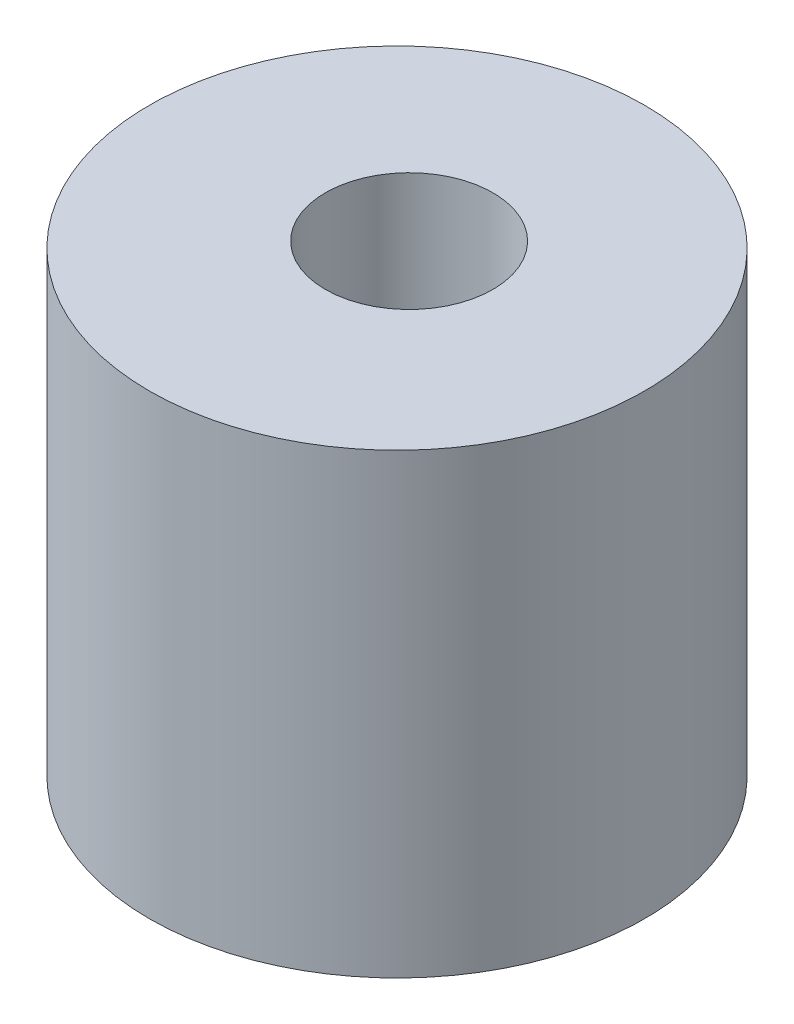
SolidWorks part; units mm, degrees
ref_plane "Plan de face" through (0, 0, 0) normal (0, 0, 1) x (1, 0, 0)
ref_plane "Plan de dessus" through (0, 0, 0) normal (0, 1, 0) x (1, 0, 0)
ref_plane "Plan de droite" through (0, 0, 0) normal (1, 0, 0) x (0, 0, -1)
sketch "Esquisse1" plane through (0, 0, 0) normal (0, 1, 0) x (1, 0, 0)
  circle A0 centre (0, 0) radius 3.25
  circle A1 centre (0, 0.1593) radius 1.1
  point P5 (0, 0)
extrude "Boss.-Extru.1" add sketch "Esquisse1" along normal blind 6
